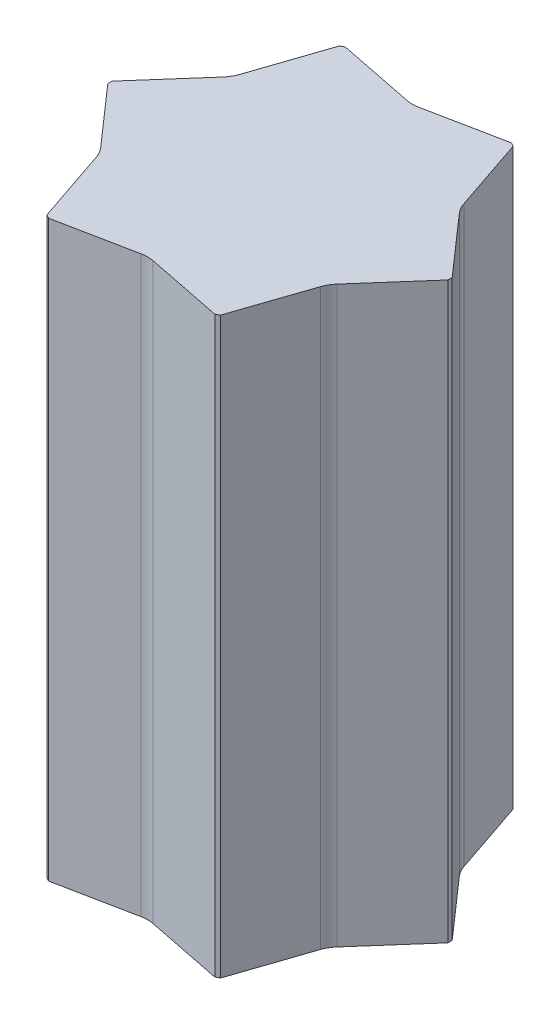
SolidWorks part; units mm, degrees
material "PEN"
ref_plane "前视基准面" through (0, 0, 0) normal (0, 0, 1) x (1, 0, 0)
ref_plane "上视基准面" through (0, 0, 0) normal (0, 1, 0) x (1, 0, 0)
ref_plane "右视基准面" through (0, 0, 0) normal (1, 0, 0) x (0, 0, -1)
sketch "草图1" plane through (0, 0, 0) normal (0, 1, 0) x (1, 0, 0)
  line L1 (395, 8.6603) -> (205, 337.7499)
  line L2 (190, 346.4102) -> (-190, 346.4102)
  line L3 (-205, 337.7499) -> (-395, 8.6603)
  line L4 (-395, -8.6603) -> (-205, -337.7499)
  line L5 (-190, -346.4102) -> (190, -346.4102)
  line L6 (205, -337.7499) -> (395, -8.6603)
  line L8 (190, 346.4102) -> (205, 337.7499)
  line L10 (395, -8.6603) -> (395, 8.6603)
  line L12 (205, -337.7499) -> (190, -346.4102)
  line L14 (-395, 8.6603) -> (-395, -8.6603)
  line L18 (-190, 346.4102) -> (-205, 337.7499)
  line L20 (-190, -346.4102) -> (-205, -337.7499)
sketch "草图4" plane through (0, 0, 0) normal (0, 1, 0) x (1, 0, 0)
  line L1 (190, 369.6203) -> (190, 346.4102)
  line L2 (11.76, 310.7841) -> (190, 346.4102)
  line L3 (-190, 346.4102) -> (-11.76, 310.7841)
  line L4 (-190, 369.6203) -> (-190, 346.4102)
  line L6 (-190, 369.6203) -> (-190, 392.8305)
  line L8 (-11.76, 428.4566) -> (-190, 392.8305)
  line L9 (190, 392.8305) -> (11.76, 428.4566)
  line L10 (190, 369.6203) -> (190, 392.8305)
  line L11 (415.1006, 20.2653) -> (395, 8.6603)
  line L17 (275.0269, 145.2076) -> (395, 8.6603)
  line L18 (205, 337.7499) -> (263.2669, 165.5765)
  line L19 (225.1006, 349.355) -> (205, 337.7499)
  line L20 (225.1006, 349.355) -> (245.2012, 360.9601)
  line L21 (365.1743, 224.4127) -> (245.2012, 360.9601)
  line L22 (435.2012, 31.8704) -> (376.9343, 204.0438)
  line L23 (415.1006, 20.2653) -> (435.2012, 31.8704)
  line L24 (225.1006, -349.355) -> (205, -337.7499)
  line L25 (263.2669, -165.5765) -> (205, -337.7499)
  line L26 (395, -8.6603) -> (275.0269, -145.2076)
  line L27 (415.1006, -20.2653) -> (395, -8.6603)
  line L28 (415.1006, -20.2653) -> (435.2012, -31.8704)
  line L29 (376.9343, -204.0438) -> (435.2012, -31.8704)
  line L30 (245.2012, -360.9601) -> (365.1743, -224.4127)
  line L31 (225.1006, -349.355) -> (245.2012, -360.9601)
  line L32 (-190, -369.6203) -> (-190, -346.4102)
  line L33 (-11.76, -310.7841) -> (-190, -346.4102)
  line L34 (190, -346.4102) -> (11.76, -310.7841)
  line L35 (190, -369.6203) -> (190, -346.4102)
  line L36 (190, -369.6203) -> (190, -392.8305)
  line L37 (11.76, -428.4566) -> (190, -392.8305)
  line L38 (-190, -392.8305) -> (-11.76, -428.4566)
  line L39 (-190, -369.6203) -> (-190, -392.8305)
  line L40 (-415.1006, -20.2653) -> (-395, -8.6603)
  line L41 (-275.0269, -145.2076) -> (-395, -8.6603)
  line L42 (-205, -337.7499) -> (-263.2669, -165.5765)
  line L43 (-225.1006, -349.355) -> (-205, -337.7499)
  line L44 (-225.1006, -349.355) -> (-245.2012, -360.9601)
  line L45 (-365.1743, -224.4127) -> (-245.2012, -360.9601)
  line L46 (-435.2012, -31.8704) -> (-376.9343, -204.0438)
  line L47 (-415.1006, -20.2653) -> (-435.2012, -31.8704)
  line L48 (-225.1006, 349.355) -> (-205, 337.7499)
  line L49 (-263.2669, 165.5765) -> (-205, 337.7499)
  line L50 (-395, 8.6603) -> (-275.0269, 145.2076)
  line L51 (-415.1006, 20.2653) -> (-395, 8.6603)
  line L52 (-415.1006, 20.2653) -> (-435.2012, 31.8704)
  line L53 (-376.9343, 204.0438) -> (-435.2012, 31.8704)
  line L54 (-245.2012, 360.9601) -> (-365.1743, 224.4127)
  line L55 (-225.1006, 349.355) -> (-245.2012, 360.9601)
  arc A0 (-11.76, 310.7841) -> (11.76, 310.7841) centre (0, 369.6203) ccw
  arc A1 (11.76, 428.4566) -> (-11.76, 428.4566) centre (0, 369.6203) ccw
  arc A2 (263.2669, 165.5765) -> (275.0269, 145.2076) centre (320.1006, 184.8102) ccw
  arc A3 (376.9343, 204.0438) -> (365.1743, 224.4127) centre (320.1006, 184.8102) ccw
  arc A4 (275.0269, -145.2076) -> (263.2669, -165.5765) centre (320.1006, -184.8102) ccw
  arc A5 (365.1743, -224.4127) -> (376.9343, -204.0438) centre (320.1006, -184.8102) ccw
  arc A8 (11.76, -310.7841) -> (-11.76, -310.7841) centre (0, -369.6203) ccw
  arc A9 (-11.76, -428.4566) -> (11.76, -428.4566) centre (0, -369.6203) ccw
  arc A10 (-263.2669, -165.5765) -> (-275.0269, -145.2076) centre (-320.1006, -184.8102) ccw
  arc A11 (-376.9343, -204.0438) -> (-365.1743, -224.4127) centre (-320.1006, -184.8102) ccw
  arc A12 (-275.0269, 145.2076) -> (-263.2669, 165.5765) centre (-320.1006, 184.8102) ccw
  arc A13 (-365.1743, 224.4127) -> (-376.9343, 204.0438) centre (-320.1006, 184.8102) ccw
  dimension "D1" = 6
sketch "草图5" plane through (0, 0, 0) normal (0, 1, 0) x (1, 0, 0)
  line L327 (-267.5147, 138.6072) -> (-385, 4.8912)
  line L328 (-385, 4.8912) -> (-385, -4.8912)
  line L329 (-385, -4.8912) -> (-267.5147, -138.6072)
  line L330 (-253.7947, -162.3709) -> (-196.7359, -330.9742)
  line L331 (-196.7359, -330.9742) -> (-188.2641, -335.8654)
  line L332 (-188.2641, -335.8654) -> (-13.72, -300.9781)
  line L333 (13.72, -300.9781) -> (188.2641, -335.8654)
  line L334 (188.2641, -335.8654) -> (196.7359, -330.9742)
  line L335 (196.7359, -330.9742) -> (253.7947, -162.3709)
  line L336 (267.5147, -138.6072) -> (385, -4.8912)
  line L337 (385, -4.8912) -> (385, 4.8912)
  line L338 (385, 4.8912) -> (267.5147, 138.6072)
  line L339 (196.7359, 330.9742) -> (188.2641, 335.8654)
  line L340 (253.7947, 162.3709) -> (196.7359, 330.9742)
  line L341 (188.2641, 335.8654) -> (13.72, 300.9781)
  line L342 (-13.72, 300.9781) -> (-188.2641, 335.8654)
  line L343 (-196.7359, 330.9742) -> (-253.7947, 162.3709)
  line L344 (-188.2641, 335.8654) -> (-196.7359, 330.9742)
  line L345 (-267.5147, 138.6072) -> (-385, 4.8912)
  line L346 (-385, 4.8912) -> (-385, -4.8912)
  line L347 (-385, -4.8912) -> (-267.5147, -138.6072)
  line L348 (-253.7947, -162.3709) -> (-196.7359, -330.9742)
  line L349 (-196.7359, -330.9742) -> (-188.2641, -335.8654)
  line L350 (-188.2641, -335.8654) -> (-13.72, -300.9781)
  line L351 (13.72, -300.9781) -> (188.2641, -335.8654)
  line L352 (188.2641, -335.8654) -> (196.7359, -330.9742)
  line L353 (196.7359, -330.9742) -> (253.7947, -162.3709)
  line L354 (267.5147, -138.6072) -> (385, -4.8912)
  line L355 (385, -4.8912) -> (385, 4.8912)
  line L356 (385, 4.8912) -> (267.5147, 138.6072)
  line L357 (196.7359, 330.9742) -> (188.2641, 335.8654)
  line L358 (253.7947, 162.3709) -> (196.7359, 330.9742)
  line L359 (188.2641, 335.8654) -> (13.72, 300.9781)
  line L360 (-13.72, 300.9781) -> (-188.2641, 335.8654)
  line L361 (-196.7359, 330.9742) -> (-253.7947, 162.3709)
  line L362 (-188.2641, 335.8654) -> (-196.7359, 330.9742)
  arc A110 (-253.7947, -162.3709) -> (-267.5147, -138.6072) centre (-320.1006, -184.8102) ccw
  arc A111 (13.72, -300.9781) -> (-13.72, -300.9781) centre (0, -369.6203) ccw
  arc A112 (267.5147, -138.6072) -> (253.7947, -162.3709) centre (320.1006, -184.8102) ccw
  arc A113 (253.7947, 162.3709) -> (267.5147, 138.6072) centre (320.1006, 184.8102) ccw
  arc A114 (-13.72, 300.9781) -> (13.72, 300.9781) centre (0, 369.6203) ccw
  arc A115 (-267.5147, 138.6072) -> (-253.7947, 162.3709) centre (-320.1006, 184.8102) ccw
  arc A116 (-253.7947, -162.3709) -> (-267.5147, -138.6072) centre (-320.1006, -184.8102) ccw
  arc A117 (13.72, -300.9781) -> (-13.72, -300.9781) centre (0, -369.6203) ccw
  arc A118 (267.5147, -138.6072) -> (253.7947, -162.3709) centre (320.1006, -184.8102) ccw
  arc A119 (253.7947, 162.3709) -> (267.5147, 138.6072) centre (320.1006, 184.8102) ccw
  arc A120 (-13.72, 300.9781) -> (13.72, 300.9781) centre (0, 369.6203) ccw
  arc A121 (-267.5147, 138.6072) -> (-253.7947, 162.3709) centre (-320.1006, 184.8102) ccw
  dimension "D1" = 10
extrude "凸台-拉伸1" add sketch "草图5" along normal mid plane 1300
